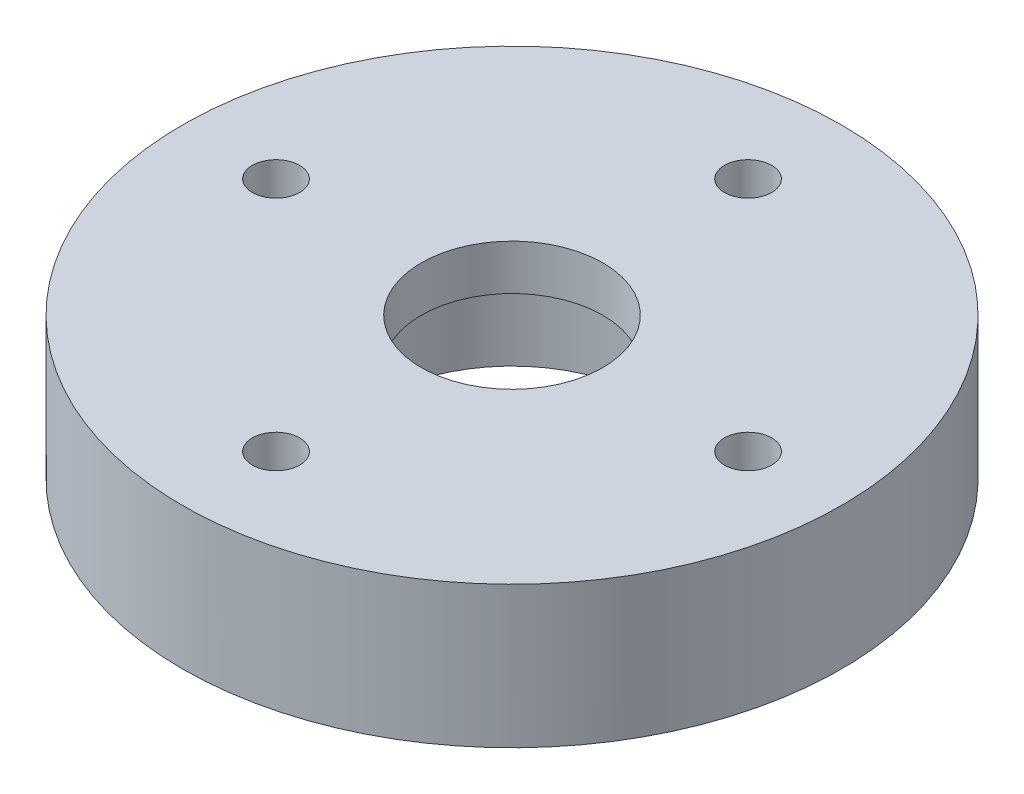
SolidWorks part; units mm, degrees
material "ABS"
ref_plane "Спереди" through (0, 0, 0) normal (0, 0, 1) x (1, 0, 0)
ref_plane "Сверху" through (0, 0, 0) normal (0, 1, 0) x (1, 0, 0)
ref_plane "Справа" through (0, 0, 0) normal (1, 0, 0) x (0, 0, -1)
sketch "Эскиз1" plane through (0, 0, 0) normal (0, 1, 0) x (1, 0, 0)
  circle A0 centre (0, 0) radius 7.6
  circle A1 centre (0, 0) radius 18.15
  dimension "D1" = 15.2
  dimension "D2" = 36.3
extrude "Бобышка-Вытянуть1" add sketch "Эскиз1" along normal blind 5.3
sketch "Эскиз8" plane through (0, 5.3, 0) normal (0, -1, 0) x (1, 0, 0)
  circle A0 centre (0, 0) radius 18.15
  circle A1 centre (0, 0) radius 5
  circle A2 centre (0, 0) radius 18.15 construction
  dimension "D1" = 10
extrude "Бобышка-Вытянуть6" add sketch "Эскиз8" against normal blind 2.5
sketch "Эскиз9" plane through (0, 7.8, 0) normal (0, 1, 0) x (1, 0, 0)
  circle A0 centre (0, 13) radius 1.3
  circle A1 centre (0, 0) radius 13 construction
  dimension "D1" = 2.6
  dimension "D2" = 26
extrude "Вырез-Вытянуть3" cut sketch "Эскиз9" against normal through all
pattern_circular "Круговой массив1" count 4 over 360 about axis through (0, 0, 0) along (0, 1, 0) of "Вырез-Вытянуть3"
